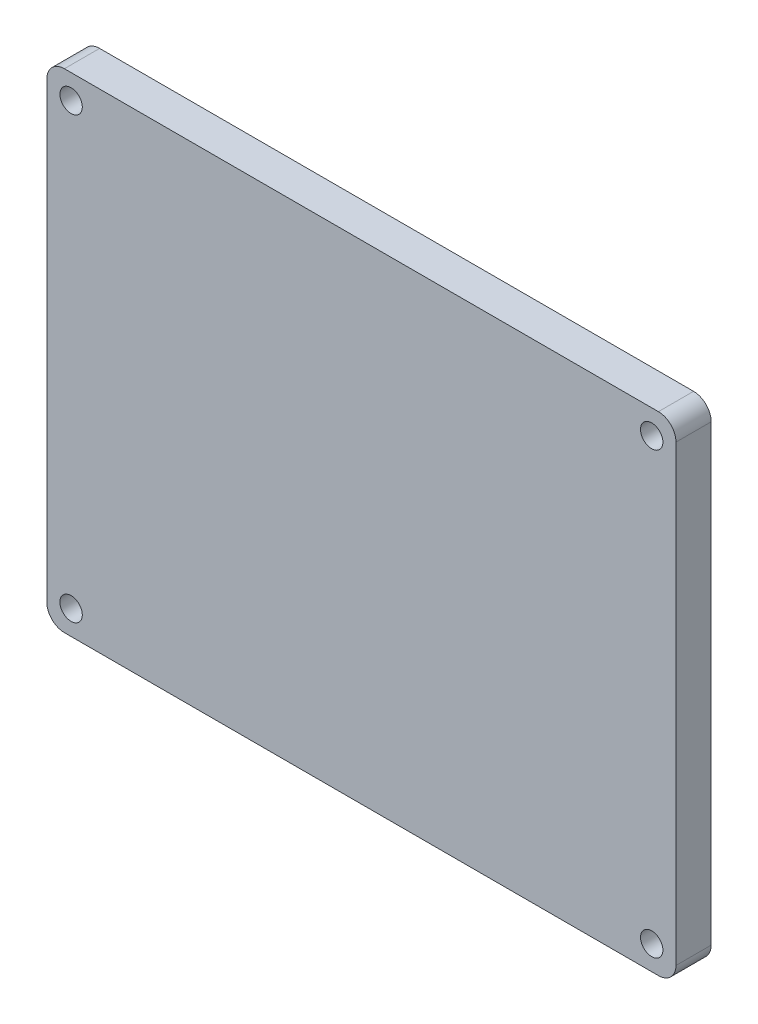
SolidWorks part; units mm, degrees
material "6061 Alloy"
ref_plane "Front Plane" through (0, 0, 0) normal (0, 0, 1) x (1, 0, 0)
ref_plane "Top Plane" through (0, 0, 0) normal (0, 1, 0) x (1, 0, 0)
ref_plane "Right Plane" through (0, 0, 0) normal (1, 0, 0) x (0, 0, -1)
sketch "Sketch1" plane through (0, 0, 0) normal (0, 0, 1) x (1, 0, 0)
  line L0 (-63.5, 0) -> (63.5, 0) construction
  line L1 (0, 50.8) -> (0, -50.8) construction
  line L3 (-56.769, 44.069) -> (56.769, 44.069)
  line L4 (-56.769, 44.069) -> (-56.769, -44.069)
  line L5 (-56.769, -44.069) -> (56.769, -44.069)
  line L6 (56.769, 44.069) -> (56.769, -44.069)
  dimension "D1" = 88.138
  dimension "D2" = 113.538
extrude "Extrude1" add sketch "Sketch1" along normal blind 6.35
sketch "Sketch2" plane through (0, 0, 6.35) normal (0, 0, 1) x (1, 0, 0)
  line L0 (-38.1902, 0) -> (38.1902, 0) construction
  line L1 (-19.05, 19.05) -> (19.05, 19.05)
  line L2 (-19.05, 19.05) -> (-19.05, -19.05)
  line L3 (-19.05, -19.05) -> (19.05, -19.05)
  line L4 (19.05, 19.05) -> (19.05, -19.05)
  line L5 (0, 28.4658) -> (0, -28.4658) construction
  dimension "D1" = 38.1
  dimension "D2" = 38.1
extrude "Cut-Extrude1" [suppressed] cut sketch "Sketch2" against normal blind 1.27
sketch "Sketch3" plane through (0, 0, 0) normal (0, 0, -1) x (-1, 0, 0)
  circle A0 centre (0, 0) radius 16.51
  dimension "D1" = 33.02
extrude "Cut-Extrude2" [suppressed] cut sketch "Sketch3" against normal up to next
sketch "Sketch6" plane through (0, 0, 6.35) normal (0, 0, 1) x (1, 0, 0)
  line L0 (-56.769, 39.6875) -> (56.769, 39.6875) construction
  line L1 (-56.769, 44.069) -> (-56.769, -44.069) construction
  line L2 (56.769, -44.069) -> (56.769, 44.069) construction
  line L3 (-56.769, -39.6875) -> (56.769, -39.6875) construction
  line L4 (52.3875, 44.069) -> (52.3875, -44.069) construction
  line L5 (56.769, 44.069) -> (-56.769, 44.069) construction
  line L6 (-56.769, -44.069) -> (56.769, -44.069) construction
  line L7 (-52.3875, 44.069) -> (-52.3875, -44.069) construction
  line L8 (-56.769, 0) -> (56.769, 0) construction
  line L9 (0, 44.069) -> (0, -44.069) construction
  dimension "D1" = 104.775
  dimension "D2" = 79.375
hole_wizard "#8 Clearance Hole1" positions "3DSketch2" profile "Sketch7" hole size "#8" standard "Ansi Inch" end condition up to next
sketch3d "3DSketch2"
  line L0 (-52.3875, 44.069, 6.35) -> (-52.3875, -44.069, 6.35) construction
  line L1 (52.3875, 44.069, 6.35) -> (52.3875, -44.069, 6.35) construction
  line L2 (-56.769, -39.6875, 6.35) -> (56.769, -39.6875, 6.35) construction
  line L3 (-56.769, 39.6875, 6.35) -> (56.769, 39.6875, 6.35) construction
  point P0 (-52.3875, 39.6875, 6.35)
  point P4 (52.3875, 39.6875, 6.35)
  point P8 (52.3875, -39.6875, 6.35)
  point P12 (-52.3875, -39.6875, 6.35)
sketch "Sketch7" plane through (-52.3875, 39.6875, 6.35) normal (1, 0, 0) x (0, -1, 0)
  line L0 (0, 0) -> (0, 6.35)
  line L1 (0, 6.35) -> (2.0193, 6.35)
  line L2 (2.0193, 6.35) -> (2.0193, 0)
  line L5 (2.0193, 0) -> (0, 0)
  line L11 (0, -6.35) -> (0, 107.95) construction
  dimension "Thru Hole Dia." = 4.0386
  dimension "Thru Hole Depth" = 6.35
sketch "Sketch8" [suppressed] plane through (0, 0, 5.08) normal (0, 0, 1) x (1, 0, 0)
  line L0 (-19.05, 14.732) -> (19.05, 14.732) construction
  line L1 (-19.05, 19.05) -> (-19.05, -19.05) construction
  line L2 (19.05, -19.05) -> (19.05, 19.05) construction
  line L3 (-19.05, -14.732) -> (19.05, -14.732) construction
  line L4 (14.732, 19.05) -> (14.732, -19.05) construction
  line L5 (19.05, 19.05) -> (-19.05, 19.05) construction
  line L6 (-19.05, -19.05) -> (19.05, -19.05) construction
  line L7 (-14.732, 19.05) -> (-14.732, -19.05) construction
  line L8 (19.05, 19.05) -> (-19.05, 19.05) construction
  line L9 (-19.05, -19.05) -> (19.05, -19.05) construction
  line L10 (-19.05, 0) -> (19.05, 0) construction
  line L11 (19.05, -19.05) -> (19.05, 19.05) construction
  line L12 (0, 19.05) -> (0, -19.05) construction
  dimension "D1" = 29.464
  dimension "D2" = 29.464
hole_wizard "#4-40 Tapped Hole2" positions "3DSketch3" profile "Sketch9" tap size "#4-40" standard "Ansi Inch"
sketch3d "3DSketch3" [suppressed]
  line L0 (-19.05, 14.732, 5.08) -> (19.05, 14.732, 5.08) construction
  line L1 (-19.05, -14.732, 5.08) -> (19.05, -14.732, 5.08) construction
  line L2 (14.732, 19.05, 5.08) -> (14.732, -19.05, 5.08) construction
  line L3 (-14.732, 19.05, 5.08) -> (-14.732, -19.05, 5.08) construction
  point P0 (-14.732, 14.732, 5.08)
  point P4 (14.732, 14.732, 5.08)
  point P6 (14.732, -14.732, 5.08)
  point P10 (-14.732, -14.732, 5.08)
sketch "Sketch9" plane through (-14.732, 14.732, 5.08) normal (1, 0, 0) x (0, -1, 0)
  line L0 (0, 0) -> (0, 3.8542)
  line L1 (0, 3.8542) -> (1.1303, 3.175)
  line L2 (1.1303, 3.175) -> (1.1303, 0)
  line L5 (1.1303, 0) -> (0, 0)
  line L10 (0, 3.8542) -> (-1.1303, 3.175) construction
  line L11 (0, -6.35) -> (0, 107.95) construction
  dimension "Tap Drill Dia." = 2.2606
  dimension "Tap Drill Depth" = 3.175
  dimension "Drill Angle" = 118
cosmetic thread "Hole Thread5" [suppressed] parameters "D1"=2.54, "D2"=2.8448
cosmetic thread "Hole Thread6" [suppressed] parameters "D1"=2.54, "D2"=2.8448
cosmetic thread "Hole Thread7" [suppressed] parameters "D1"=2.54, "D2"=2.8448
cosmetic thread "Hole Thread8" [suppressed] parameters "D1"=2.54, "D2"=2.8448
sketch "Sketch10" plane through (0, 0, 0) normal (0, 0, -1) x (-1, 0, 0)
  line L0 (-56.769, 29.21) -> (56.769, 29.21) construction
  line L1 (-56.769, -44.069) -> (-56.769, 44.069) construction
  line L2 (56.769, 44.069) -> (56.769, -44.069) construction
  line L3 (-56.769, -29.21) -> (56.769, -29.21) construction
  line L4 (41.91, 44.069) -> (41.91, -44.069) construction
  line L5 (-56.769, 44.069) -> (56.769, 44.069) construction
  line L6 (56.769, -44.069) -> (-56.769, -44.069) construction
  line L7 (-41.91, 44.069) -> (-41.91, -44.069) construction
  line L8 (-56.769, 0) -> (56.769, 0) construction
  line L9 (0, 44.069) -> (0, -44.069) construction
  dimension "D1" = 58.42
  dimension "D2" = 83.82
hole_wizard "#4-40 Tapped Hole3" positions "3DSketch4" profile "Sketch11" tap size "#4-40" standard "Ansi Inch"
sketch3d "3DSketch4"
  line L0 (41.91, 44.069, 0) -> (41.91, -44.069, 0) construction
  line L1 (-41.91, 44.069, 0) -> (-41.91, -44.069, 0) construction
  line L2 (56.769, 29.21, 0) -> (-56.769, 29.21, 0) construction
  line L3 (56.769, -29.21, 0) -> (-56.769, -29.21, 0) construction
  point P0 (41.91, 29.21, 0)
  point P4 (-41.91, 29.21, 0)
  point P8 (-41.91, -29.21, 0)
  point P10 (41.91, -29.21, 0)
sketch "Sketch11" plane through (41.91, 29.21, 0) normal (1, 0, 0) x (0, 1, 0)
  line L0 (0, 0) -> (0, 5.1242)
  line L1 (0, 5.1242) -> (1.1303, 4.445)
  line L2 (1.1303, 4.445) -> (1.1303, 0)
  line L5 (1.1303, 0) -> (0, 0)
  line L10 (0, 5.1242) -> (-1.1303, 4.445) construction
  line L11 (0, -6.35) -> (0, 107.95) construction
  dimension "Tap Drill Dia." = 2.2606
  dimension "Tap Drill Depth" = 4.445
  dimension "Drill Angle" = 118
cosmetic thread "Hole Thread9" [suppressed] parameters "D1"=3.81, "D2"=2.8448
cosmetic thread "Hole Thread10" [suppressed] parameters "D1"=3.81, "D2"=2.8448
cosmetic thread "Hole Thread11" [suppressed] parameters "D1"=3.81, "D2"=2.8448
cosmetic thread "Hole Thread12" [suppressed] parameters "D1"=3.81, "D2"=2.8448
fillet "Fillet1" [suppressed] radius 1.27
fillet "Fillet2" radius 3.175 4 edges at (-56.769, -44.069, 3.175) (56.769, -44.069, 3.175) (56.769, 44.069, 3.175) (-56.769, 44.069, 3.175)
